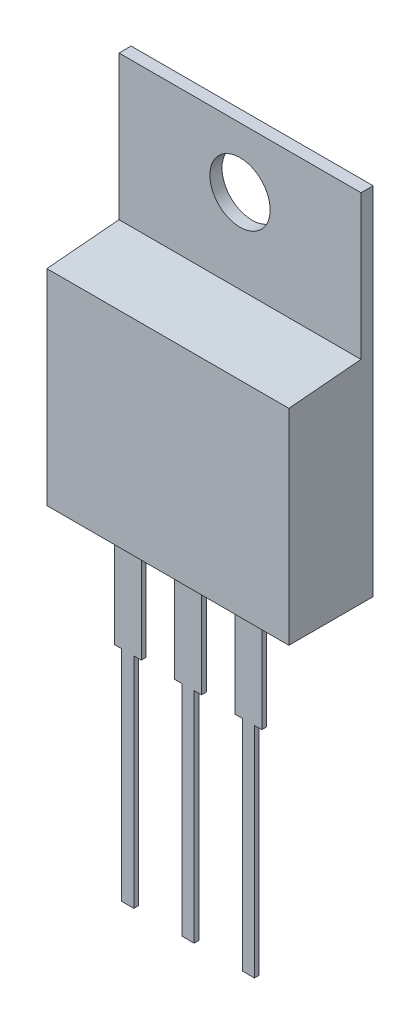
SolidWorks part; units mm, degrees
ref_plane "Front Plane" through (0, 0, 0) normal (0, 0, 1) x (1, 0, 0)
ref_plane "Top Plane" through (0, 0, 0) normal (0, 1, 0) x (1, 0, 0)
ref_plane "Right Plane" through (0, 0, 0) normal (1, 0, 0) x (0, 0, -1)
sketch "Sketch1" plane through (0, 0, 0) normal (0, 0, 1) x (1, 0, 0)
  line L1 (0, 0) -> (10.2, 0)
  line L2 (0, 0) -> (0, 15)
  line L3 (0, 15) -> (10.2, 15)
  line L4 (10.2, 0) -> (10.2, 15)
  dimension "D1" = 15
  dimension "D2" = 10.2
extrude "Boss-Extrude1" add sketch "Sketch1" along normal blind 0.51
sketch "Sketch2" plane through (0, 0, 0.51) normal (0, 0, 1) x (1, 0, 0)
  line L0 (10.2, 0) -> (10.2, 15) construction
  line L1 (0, 0) -> (10.2, 0)
  line L2 (0, 0) -> (0, 8.65)
  line L3 (0, 8.65) -> (10.2, 8.65)
  line L4 (10.2, 0) -> (10.2, 8.65)
  line L5 (10.2, 15) -> (0, 15) construction
  dimension "D1" = 6.35
extrude "Boss-Extrude2" add sketch "Sketch2" along normal blind 3.04
draft "Draft1" type of draft neutral plane draft angle 5 faces to draft 1 face at (6.375, 8.65, 2.79) neutral plane through (0, 0, 3.55) neutral plane normal (0, 0, 1) parameters "D1"=5
ref_plane "Plane1" through (2.56, 0, 0) normal (-1, 0, 0) x (0, 0, 1)
sketch "Sketch3" plane through (2.56, 0, 0) normal (-1, 0, 0) x (0, 0, 1)
  line L0 (2.5, 0) -> (2.5, -4.5)
  line L1 (3.55, 0) -> (0, 0) construction
  line L2 (0, 15) -> (0, 0) construction
  dimension "D1" = 4.5
  dimension "D2" = 2.5
extrude "Extrude-Thin1" add sketch "Sketch3" along normal mid plane 1.14 thin thin type one direction reverse wall 0.2
sketch "Sketch4" plane through (2.56, 0, 0) normal (-1, 0, 0) x (0, 0, 1)
  line L0 (2.5, -4.5) -> (2.5, -13.72)
  line L1 (3.55, 0) -> (0, 0) construction
  dimension "D1" = 13.72
extrude "Extrude-Thin2" add sketch "Sketch4" along normal mid plane 0.51 thin thin type one direction reverse wall 0.2
pattern_linear "LPattern1" count 3 spacing 2.54 along (1, 0, 0) of "Extrude-Thin1", "Extrude-Thin2"
sketch "Sketch5" plane through (0, 0, 0.51) normal (0, 0, 1) x (1, 0, 0)
  line L0 (10.2, 15) -> (0, 15) construction
  circle A0 centre (5.1, 12.46) radius 1.27
  dimension "D2" = 2.54
  dimension "D1" = 2.54
extrude "Cut-Extrude1" cut sketch "Sketch5" against normal up to next
